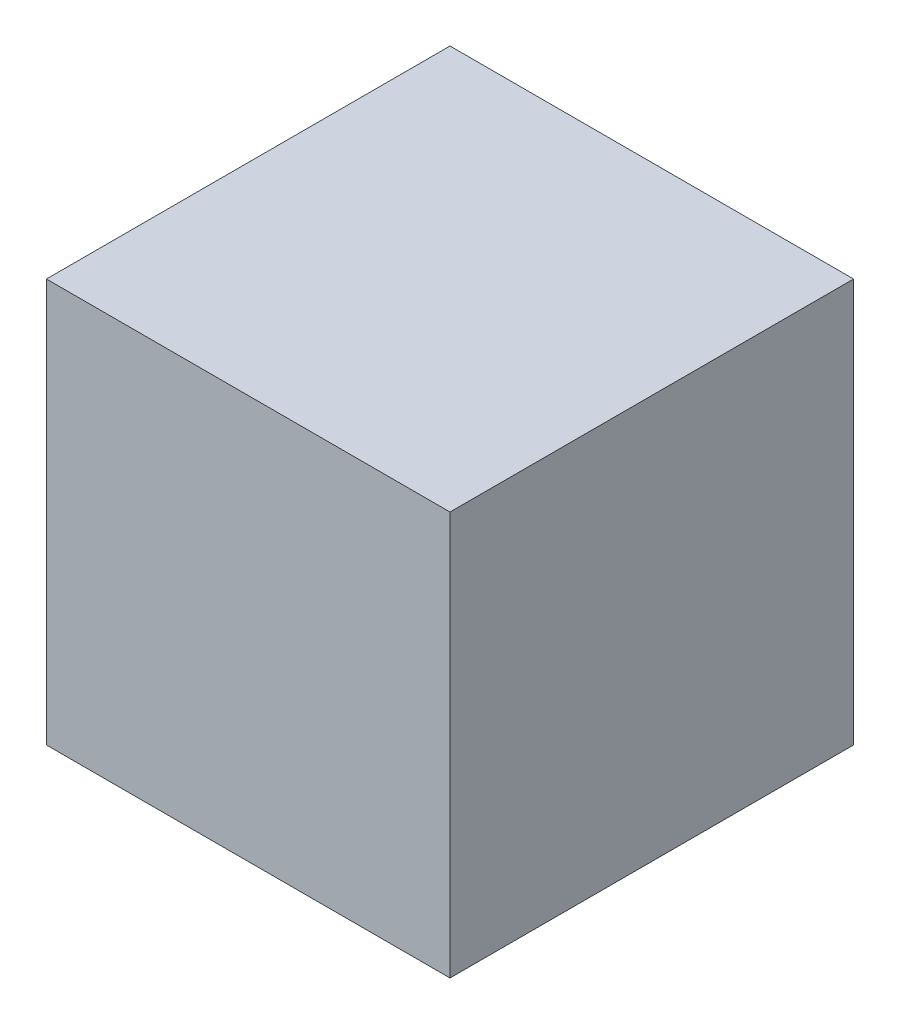
SolidWorks part; units mm, degrees
ref_plane "Front Plane" through (0, 0, 0) normal (0, 0, 1) x (1, 0, 0)
ref_plane "Top Plane" through (0, 0, 0) normal (0, 1, 0) x (1, 0, 0)
ref_plane "Right Plane" through (0, 0, 0) normal (1, 0, 0) x (0, 0, -1)
sketch "Sketch1" plane through (0, 0, 0) normal (0, 1, 0) x (1, 0, 0)
  line L1 (50, -50) -> (-50, -50)
  line L2 (50, -50) -> (50, 50)
  line L3 (50, 50) -> (-50, 50)
  line L4 (-50, -50) -> (-50, 50)
  line L5 (50, -50) -> (-50, 50) construction
  line L6 (50, 50) -> (-50, -50) construction
  point P0 (0, 0)
  dimension "D1" = 100
extrude "Boss-Extrude1" add sketch "Sketch1" along normal blind 100 contours L3 L4 L1 L2
